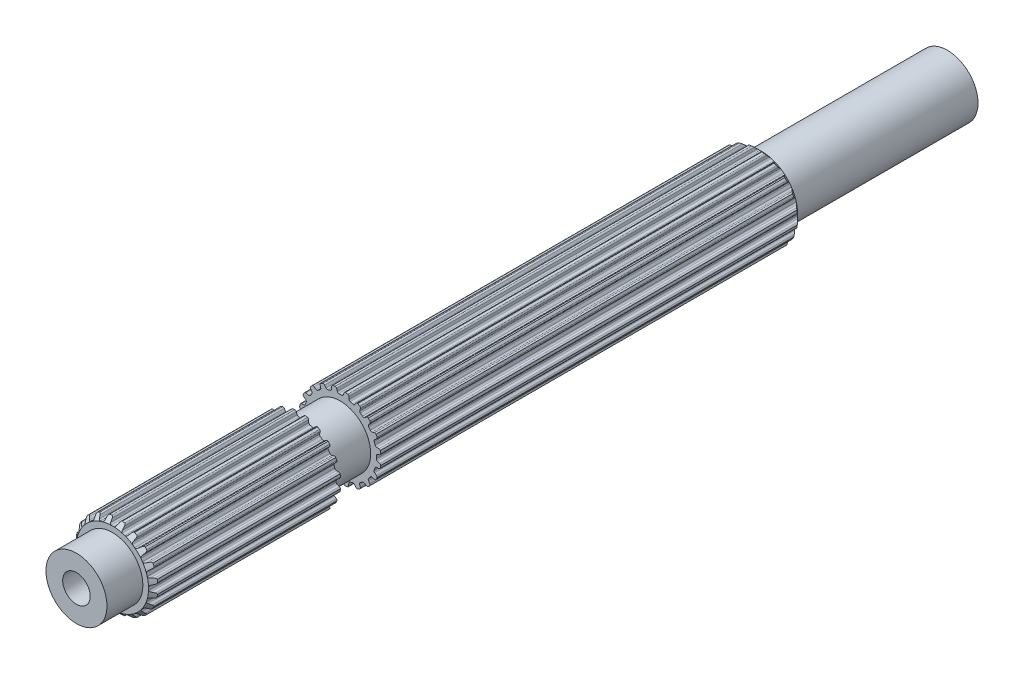
SolidWorks part; units mm, degrees
ref_plane "Front Plane" through (0, 0, 0) normal (0, 0, 1) x (1, 0, 0)
ref_plane "Top Plane" through (0, 0, 0) normal (0, 1, 0) x (1, 0, 0)
ref_plane "Right Plane" through (0, 0, 0) normal (1, 0, 0) x (0, 0, -1)
sketch "Sketch1" plane through (0, 0, 0) normal (0, 0, 1) x (1, 0, 0)
  line L0 (-0.1069, 2.9699) -> (0.1069, 2.9699)
  line L1 (0.3159, 3.2375) -> (0.2537, 3.0575)
  line L2 (-0.2964, 3.2367) -> (-0.2318, 3.0575)
  line L3 (-0.2964, 3.2367) -> (0.3159, 3.2375) construction
  line L4 (0, 3.3252) -> (0, 0) construction
  line L5 (-0.2318, 3.0575) -> (0.2537, 3.0575) construction
  line L6 (-0.4281, 3.3241) -> (0.4281, 3.3263) construction
  line L7 (0.7183, 3.1698) -> (0.7244, 2.9795)
  line L8 (0.816, 2.8576) -> (1.0195, 2.7915)
  line L9 (1.3009, 2.9815) -> (1.1862, 2.8295)
  line L10 (1.6627, 2.7927) -> (1.6097, 2.6099)
  line L11 (1.6591, 2.4655) -> (1.8322, 2.3398)
  line L12 (2.1585, 2.4335) -> (2.0025, 2.3245)
  line L13 (2.4443, 2.1423) -> (2.3374, 1.9847)
  line L14 (2.3398, 1.8322) -> (2.4655, 1.6591)
  line L15 (2.8049, 1.6474) -> (2.6228, 1.5919)
  line L16 (2.9866, 1.2821) -> (2.8363, 1.1653)
  line L17 (2.7915, 1.0195) -> (2.8576, 0.816)
  line L18 (3.1767, 0.7) -> (2.9863, 0.7035)
  line L19 (3.2367, 0.2964) -> (3.0575, 0.2318)
  line L20 (2.9699, 0.1069) -> (2.9699, -0.1069)
  line L21 (3.2375, -0.3159) -> (3.0575, -0.2537)
  line L22 (3.1698, -0.7183) -> (2.9795, -0.7244)
  line L23 (2.8576, -0.816) -> (2.7915, -1.0195)
  line L24 (2.9815, -1.3009) -> (2.8295, -1.1862)
  line L25 (2.7927, -1.6627) -> (2.6099, -1.6097)
  line L26 (2.4655, -1.6591) -> (2.3398, -1.8322)
  line L27 (2.4335, -2.1585) -> (2.3245, -2.0025)
  line L28 (2.1423, -2.4443) -> (1.9847, -2.3374)
  line L29 (1.8322, -2.3398) -> (1.6591, -2.4655)
  line L30 (1.6474, -2.8049) -> (1.5919, -2.6228)
  line L31 (1.2821, -2.9866) -> (1.1653, -2.8363)
  line L32 (1.0195, -2.7915) -> (0.816, -2.8576)
  line L33 (0.7, -3.1767) -> (0.7035, -2.9863)
  line L34 (0.2964, -3.2367) -> (0.2318, -3.0575)
  line L35 (0.1069, -2.9699) -> (-0.1069, -2.9699)
  line L36 (-0.3159, -3.2375) -> (-0.2537, -3.0575)
  line L37 (-0.7183, -3.1698) -> (-0.7244, -2.9795)
  line L38 (-0.816, -2.8576) -> (-1.0195, -2.7915)
  line L39 (-1.3009, -2.9815) -> (-1.1862, -2.8295)
  line L40 (-1.6627, -2.7927) -> (-1.6097, -2.6099)
  line L41 (-1.6591, -2.4655) -> (-1.8322, -2.3398)
  line L42 (-2.1585, -2.4335) -> (-2.0025, -2.3245)
  line L43 (-2.4443, -2.1423) -> (-2.3374, -1.9847)
  line L44 (-2.3398, -1.8322) -> (-2.4655, -1.6591)
  line L45 (-2.8049, -1.6474) -> (-2.6228, -1.5919)
  line L46 (-2.9866, -1.2821) -> (-2.8363, -1.1653)
  line L47 (-2.7915, -1.0195) -> (-2.8576, -0.816)
  line L48 (-3.1767, -0.7) -> (-2.9863, -0.7035)
  line L49 (-3.2367, -0.2964) -> (-3.0575, -0.2318)
  line L50 (-2.9699, -0.1069) -> (-2.9699, 0.1069)
  line L51 (-3.2375, 0.3159) -> (-3.0575, 0.2537)
  line L52 (-3.1698, 0.7183) -> (-2.9795, 0.7244)
  line L53 (-2.8576, 0.816) -> (-2.7915, 1.0195)
  line L54 (-2.9815, 1.3009) -> (-2.8295, 1.1862)
  line L55 (-2.7927, 1.6627) -> (-2.6099, 1.6097)
  line L56 (-2.4655, 1.6591) -> (-2.3398, 1.8322)
  line L57 (-2.4335, 2.1585) -> (-2.3245, 2.0025)
  line L58 (-2.1423, 2.4443) -> (-1.9847, 2.3374)
  line L59 (-1.8322, 2.3398) -> (-1.6591, 2.4655)
  line L60 (-1.6474, 2.8049) -> (-1.5919, 2.6228)
  line L61 (-1.2821, 2.9866) -> (-1.1653, 2.8363)
  line L62 (-1.0195, 2.7915) -> (-0.816, 2.8576)
  line L63 (-0.7, 3.1767) -> (-0.7035, 2.9863)
  line L64 (0.4281, 3.3263) -> (0.62, 3.2938)
  line L65 (1.4351, 3.0312) -> (1.6075, 2.9409)
  line L66 (2.3015, 2.4394) -> (2.4376, 2.3003)
  line L67 (2.9427, 1.6088) -> (3.0291, 1.4344)
  line L68 (3.2958, 0.6207) -> (3.3241, 0.4281)
  line L69 (3.3263, -0.4281) -> (3.2938, -0.62)
  line L70 (3.0312, -1.4351) -> (2.9409, -1.6075)
  line L71 (2.4394, -2.3015) -> (2.3003, -2.4376)
  line L72 (1.6088, -2.9427) -> (1.4344, -3.0291)
  line L73 (0.6207, -3.2958) -> (0.4281, -3.3241)
  line L74 (-0.4281, -3.3263) -> (-0.62, -3.2938)
  line L75 (-1.4351, -3.0312) -> (-1.6075, -2.9409)
  line L76 (-2.3015, -2.4394) -> (-2.4376, -2.3003)
  line L77 (-2.9427, -1.6088) -> (-3.0291, -1.4344)
  line L78 (-3.2958, -0.6207) -> (-3.3241, -0.4281)
  line L79 (-3.3263, 0.4281) -> (-3.2938, 0.62)
  line L80 (-3.0312, 1.4351) -> (-2.9409, 1.6075)
  line L81 (-2.4394, 2.3015) -> (-2.3003, 2.4376)
  line L82 (-1.6088, 2.9427) -> (-1.4344, 3.0291)
  line L83 (-0.6207, 3.2958) -> (-0.4281, 3.3241)
  arc A0 (0.2537, 3.0575) -> (0.1069, 2.9699) centre (0.1283, 3.1009) cw
  arc A1 (-0.2318, 3.0575) -> (-0.1069, 2.9699) centre (-0.1069, 3.1026) ccw
  arc A2 (0.62, 3.2938) -> (0.7183, 3.1698) centre (0.5856, 3.1656) cw
  arc A3 (0.7244, 2.9795) -> (0.816, 2.8576) centre (0.857, 2.9838) ccw
  arc A4 (-0.4281, 3.3241) -> (-0.2964, 3.2367) centre (-0.4213, 3.1916) cw
  arc A5 (0.4281, 3.3263) -> (0.3159, 3.2375) centre (0.4413, 3.1942) ccw
  arc A6 (1.1862, 2.8295) -> (1.0195, 2.7915) centre (1.0802, 2.9095) cw
  arc A7 (1.4351, 3.0312) -> (1.3009, 2.9815) centre (1.4068, 2.9015) ccw
  arc A8 (1.6075, 2.9409) -> (1.6627, 2.7927) centre (1.5352, 2.8297) cw
  arc A9 (1.6097, 2.6099) -> (1.6591, 2.4655) centre (1.7371, 2.5729) ccw
  arc A10 (2.0025, 2.3245) -> (1.8322, 2.3398) centre (1.9264, 2.4332) cw
  arc A11 (2.3015, 2.4394) -> (2.1585, 2.4335) centre (2.2346, 2.3248) ccw
  arc A12 (2.4376, 2.3003) -> (2.4443, 2.1423) centre (2.3345, 2.2168) cw
  arc A13 (2.3374, 1.9847) -> (2.3398, 1.8322) centre (2.4472, 1.9102) ccw
  arc A14 (2.6228, 1.5919) -> (2.4655, 1.6591) centre (2.5841, 1.7189) cw
  arc A15 (2.9427, 1.6088) -> (2.8049, 1.6474) centre (2.8436, 1.5205) ccw
  arc A16 (3.0291, 1.4344) -> (2.9866, 1.2821) centre (2.9052, 1.3869) cw
  arc A17 (2.8363, 1.1653) -> (2.7915, 1.0195) centre (2.9177, 1.0605) ccw
  arc A18 (2.9863, 0.7035) -> (2.8576, 0.816) centre (2.9887, 0.8362) cw
  arc A19 (3.2958, 0.6207) -> (3.1767, 0.7) centre (3.1743, 0.5673) ccw
  arc A20 (3.3241, 0.4281) -> (3.2367, 0.2964) centre (3.1916, 0.4213) cw
  arc A21 (3.0575, 0.2318) -> (2.9699, 0.1069) centre (3.1026, 0.1069) ccw
  arc A22 (3.0575, -0.2537) -> (2.9699, -0.1069) centre (3.1009, -0.1283) cw
  arc A23 (3.3263, -0.4281) -> (3.2375, -0.3159) centre (3.1942, -0.4413) ccw
  arc A24 (3.2938, -0.62) -> (3.1698, -0.7183) centre (3.1656, -0.5856) cw
  arc A25 (2.9795, -0.7244) -> (2.8576, -0.816) centre (2.9838, -0.857) ccw
  arc A26 (2.8295, -1.1862) -> (2.7915, -1.0195) centre (2.9095, -1.0802) cw
  arc A27 (3.0312, -1.4351) -> (2.9815, -1.3009) centre (2.9015, -1.4068) ccw
  arc A28 (2.9409, -1.6075) -> (2.7927, -1.6627) centre (2.8297, -1.5352) cw
  arc A29 (2.6099, -1.6097) -> (2.4655, -1.6591) centre (2.5729, -1.7371) ccw
  arc A30 (2.3245, -2.0025) -> (2.3398, -1.8322) centre (2.4332, -1.9264) cw
  arc A31 (2.4394, -2.3015) -> (2.4335, -2.1585) centre (2.3248, -2.2346) ccw
  arc A32 (2.3003, -2.4376) -> (2.1423, -2.4443) centre (2.2168, -2.3345) cw
  arc A33 (1.9847, -2.3374) -> (1.8322, -2.3398) centre (1.9102, -2.4472) ccw
  arc A34 (1.5919, -2.6228) -> (1.6591, -2.4655) centre (1.7189, -2.5841) cw
  arc A35 (1.6088, -2.9427) -> (1.6474, -2.8049) centre (1.5205, -2.8436) ccw
  arc A36 (1.4344, -3.0291) -> (1.2821, -2.9866) centre (1.3869, -2.9052) cw
  arc A37 (1.1653, -2.8363) -> (1.0195, -2.7915) centre (1.0605, -2.9177) ccw
  arc A38 (0.7035, -2.9863) -> (0.816, -2.8576) centre (0.8362, -2.9887) cw
  arc A39 (0.6207, -3.2958) -> (0.7, -3.1767) centre (0.5673, -3.1743) ccw
  arc A40 (0.4281, -3.3241) -> (0.2964, -3.2367) centre (0.4213, -3.1916) cw
  arc A41 (0.2318, -3.0575) -> (0.1069, -2.9699) centre (0.1069, -3.1026) ccw
  arc A42 (-0.2537, -3.0575) -> (-0.1069, -2.9699) centre (-0.1283, -3.1009) cw
  arc A43 (-0.4281, -3.3263) -> (-0.3159, -3.2375) centre (-0.4413, -3.1942) ccw
  arc A44 (-0.62, -3.2938) -> (-0.7183, -3.1698) centre (-0.5856, -3.1656) cw
  arc A45 (-0.7244, -2.9795) -> (-0.816, -2.8576) centre (-0.857, -2.9838) ccw
  arc A46 (-1.1862, -2.8295) -> (-1.0195, -2.7915) centre (-1.0802, -2.9095) cw
  arc A47 (-1.4351, -3.0312) -> (-1.3009, -2.9815) centre (-1.4068, -2.9015) ccw
  arc A48 (-1.6075, -2.9409) -> (-1.6627, -2.7927) centre (-1.5352, -2.8297) cw
  arc A49 (-1.6097, -2.6099) -> (-1.6591, -2.4655) centre (-1.7371, -2.5729) ccw
  arc A50 (-2.0025, -2.3245) -> (-1.8322, -2.3398) centre (-1.9264, -2.4332) cw
  arc A51 (-2.3015, -2.4394) -> (-2.1585, -2.4335) centre (-2.2346, -2.3248) ccw
  arc A52 (-2.4376, -2.3003) -> (-2.4443, -2.1423) centre (-2.3345, -2.2168) cw
  arc A53 (-2.3374, -1.9847) -> (-2.3398, -1.8322) centre (-2.4472, -1.9102) ccw
  arc A54 (-2.6228, -1.5919) -> (-2.4655, -1.6591) centre (-2.5841, -1.7189) cw
  arc A55 (-2.9427, -1.6088) -> (-2.8049, -1.6474) centre (-2.8436, -1.5205) ccw
  arc A56 (-3.0291, -1.4344) -> (-2.9866, -1.2821) centre (-2.9052, -1.3869) cw
  arc A57 (-2.8363, -1.1653) -> (-2.7915, -1.0195) centre (-2.9177, -1.0605) ccw
  arc A58 (-2.9863, -0.7035) -> (-2.8576, -0.816) centre (-2.9887, -0.8362) cw
  arc A59 (-3.2958, -0.6207) -> (-3.1767, -0.7) centre (-3.1743, -0.5673) ccw
  arc A60 (-3.3241, -0.4281) -> (-3.2367, -0.2964) centre (-3.1916, -0.4213) cw
  arc A61 (-3.0575, -0.2318) -> (-2.9699, -0.1069) centre (-3.1026, -0.1069) ccw
  arc A62 (-3.0575, 0.2537) -> (-2.9699, 0.1069) centre (-3.1009, 0.1283) cw
  arc A63 (-3.3263, 0.4281) -> (-3.2375, 0.3159) centre (-3.1942, 0.4413) ccw
  arc A64 (-3.2938, 0.62) -> (-3.1698, 0.7183) centre (-3.1656, 0.5856) cw
  arc A65 (-2.9795, 0.7244) -> (-2.8576, 0.816) centre (-2.9838, 0.857) ccw
  arc A66 (-2.8295, 1.1862) -> (-2.7915, 1.0195) centre (-2.9095, 1.0802) cw
  arc A67 (-3.0312, 1.4351) -> (-2.9815, 1.3009) centre (-2.9015, 1.4068) ccw
  arc A68 (-2.9409, 1.6075) -> (-2.7927, 1.6627) centre (-2.8297, 1.5352) cw
  arc A69 (-2.6099, 1.6097) -> (-2.4655, 1.6591) centre (-2.5729, 1.7371) ccw
  arc A70 (-2.3245, 2.0025) -> (-2.3398, 1.8322) centre (-2.4332, 1.9264) cw
  arc A71 (-2.4394, 2.3015) -> (-2.4335, 2.1585) centre (-2.3248, 2.2346) ccw
  arc A72 (-2.3003, 2.4376) -> (-2.1423, 2.4443) centre (-2.2168, 2.3345) cw
  arc A73 (-1.9847, 2.3374) -> (-1.8322, 2.3398) centre (-1.9102, 2.4472) ccw
  arc A74 (-1.5919, 2.6228) -> (-1.6591, 2.4655) centre (-1.7189, 2.5841) cw
  arc A75 (-1.6088, 2.9427) -> (-1.6474, 2.8049) centre (-1.5205, 2.8436) ccw
  arc A76 (-1.4344, 3.0291) -> (-1.2821, 2.9866) centre (-1.3869, 2.9052) cw
  arc A77 (-1.1653, 2.8363) -> (-1.0195, 2.7915) centre (-1.0605, 2.9177) ccw
  arc A78 (-0.7035, 2.9863) -> (-0.816, 2.8576) centre (-0.8362, 2.9887) cw
  arc A79 (-0.6207, 3.2958) -> (-0.7, 3.1767) centre (-0.5673, 3.1743) ccw
  point P14 (0, 2.9699)
  point P247 (0, 0)
  dimension "D4" = 0.1327
  dimension "D8" = 20
  dimension "D1" = 2.9699
  dimension "D2" = 0.2139
  dimension "D3" = 0.1904
  dimension "D5" = 0.0877
  dimension "D6" = 0.4855
  dimension "D7" = 0.8563
extrude "Boss-Extrude1" add sketch "Sketch1" along normal blind 15.3822 and the other way blind 37.846
sketch "Sketch2" plane through (0, 0, 0) normal (0, 0, 1) x (1, 0, 0)
  circle A0 centre (0, 0) radius 2.5019
  dimension "D1" = 5.0038
extrude "Boss-Extrude2" add sketch "Sketch2" along normal blind 18.3286 and the other way blind 53.1114
sketch "Sketch4" plane through (0, 0, 18.3286) normal (0, 0, 1) x (1, 0, 0)
  circle A0 centre (0, 0) radius 2.5019 construction
  point P0 (0, 0)
sketch "Sketch5" plane through (0, 0, -53.1114) normal (0, 0, -1) x (-1, 0, 0)
  circle A0 centre (0, 0) radius 2.5019 construction
  point P0 (0, 0)
sketch "Sketch3" plane through (0, 0, 0) normal (1, 0, 0) x (0, 0, -1)
  line L0 (-14.251, 4.1011) -> (-15.3822, 2.9699)
  line L1 (-15.3822, 2.9699) -> (-15.3822, 4.1011)
  line L2 (-15.3822, 4.1011) -> (-14.251, 4.1011)
  line L3 (-15.3822, 2.5019) -> (-15.3822, -2.5019) construction
  line L5 (-14.3608, 0) -> (13.2171, 0) construction
  line L7 (37.846, 34.5599) -> (37.846, 2.9699)
  line L8 (37.846, 2.9699) -> (22.051, 18.7649)
  line L9 (22.051, 18.7649) -> (37.846, 34.5599)
  line L10 (37.846, -2.5019) -> (37.846, 2.5019) construction
  point P6 (-4.866, 6.1438)
  dimension "D1" = 45
  dimension "D2" = 45
revolve "Cut-Revolve1" cut sketch "Sketch3" angle 360 about L5
sketch "Sketch7" plane through (0, 0, 0) normal (0, 0, 1) x (1, 0, 0)
  circle A0 centre (0, 0) radius 1.1303
  dimension "D1" = 2.2606
extrude "Cut-Extrude1" cut sketch "Sketch7" along normal up to surface and the other way up to surface up to face at (2.5019, 0, 18.3286) other way up to face at (2.5019, 0, -53.1114)
sketch "Sketch8" plane through (0, 0, 0) normal (0, 0, 1) x (1, 0, 0)
  circle A0 centre (0, 0) radius 1.1303
  circle A1 centre (0, 0) radius 1.1303 construction
extrude "Boss-Extrude3" add sketch "Sketch8" along normal offset from surface 9.525 and the other way offset from surface (43.5864 mm away) 9.525 up to face at (1.1303, 0, 18.3286) other way up to face at (1.1303, 0, -53.1114)
sketch "Sketch9" plane through (0, 0, 0) normal (0, 0, 1) x (1, 0, 0)
  circle A0 centre (0, 0) radius 2.5019
  circle A2 centre (0, 0) radius 6.7879
  dimension "D1" = 5.0038
extrude "Cut-Extrude2" cut sketch "Sketch9" against normal blind 3.302
